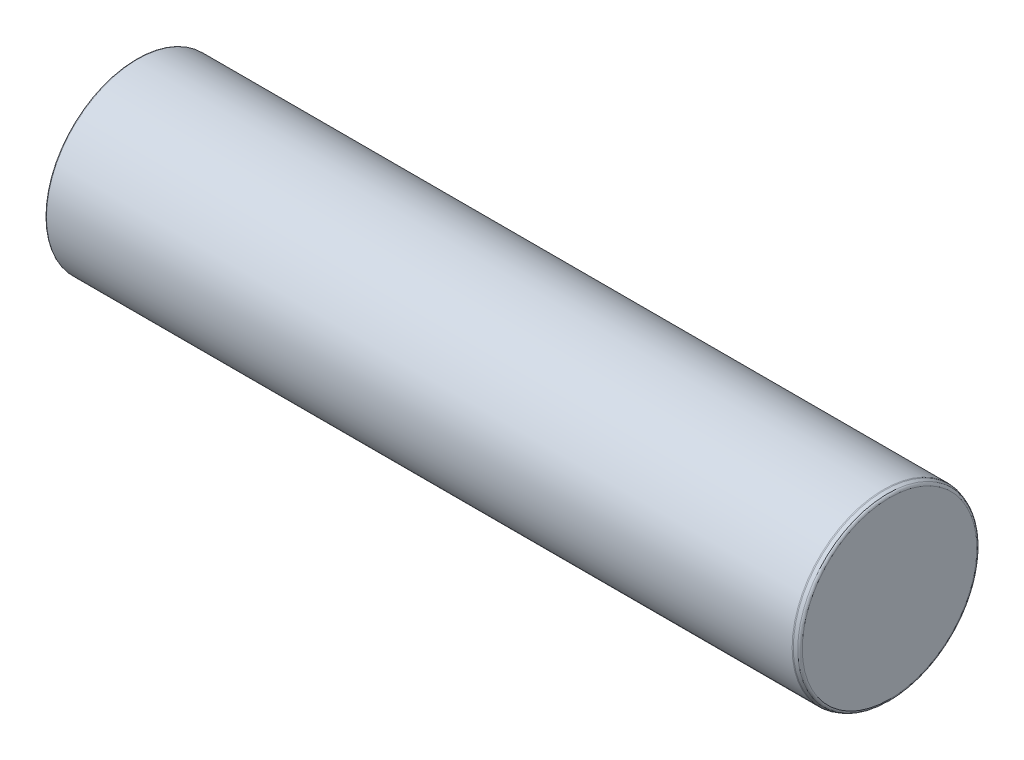
SolidWorks part; units mm, degrees
revolve "Base-Revolve" add sketch "Sketch1" angle 360 about L0
sketch "Sketch1" plane through (0, 0, 0) normal (0, 0, 1) x (1, 0, 0)
  line L0 (-136.5, 0) -> (136.5, 0) construction
  line L1 (134.3237, 32.5) -> (-0.0001, 32.5)
  line L4 (-113.5555, 0) -> (136.5, 0)
  line L5 (135.842, 32.0115) -> (134.6657, 32.4397)
  line L6 (-131.5, 32.1) -> (-131.5, 28.4)
  line L7 (-136.5, 5.1) -> (-116.5, 5.1)
  line L8 (-116.5, 5.1) -> (-113.5555, 0)
  line L13 (-0.0001, 32.5) -> (-131.1, 32.5)
  line L17 (-132.7, 24.8845) -> (-136.3, 22.8061)
  line L19 (-132.5, 28) -> (-132.5, 25.2309)
  line L20 (-136.5, 22.4597) -> (-136.5, 5.1)
  line L21 (-131.9, 28) -> (-132.5, 28)
  line L22 (136.5, 31.0719) -> (136.5, 0)
  arc A0 (136.5, 31.0719) -> (135.842, 32.0115) centre (135.5, 31.0719) ccw
  arc A1 (-131.9, 28) -> (-131.5, 28.4) centre (-131.9, 28.4) ccw
  arc A2 (134.6657, 32.4397) -> (134.3237, 32.5) centre (134.3237, 31.5) ccw
  arc A3 (-136.3, 22.8061) -> (-136.5, 22.4597) centre (-136.1, 22.4597) ccw
  arc A4 (-132.7, 24.8845) -> (-132.5, 25.2309) centre (-132.9, 25.2309) ccw
  arc A5 (-131.5, 32.1) -> (-131.1, 32.5) centre (-131.1, 32.1) cw
  point P5 (136.5, 31.7721)
  point P15 (134.5, 32.5)
  point P28 (-132.5, 25)
  point P31 (-131.5, 32.5)
  dimension "D11" = 50
  dimension "D17" = 1
  dimension "D19" = 0.4
  dimension "D3" = 2
  dimension "D4" = 20
  dimension "D5" = 273
  dimension "D7" = 5
  dimension "D8" = 1
  dimension "D9" = 56
  dimension "D10" = 30
  dimension "D12" = 65
  dimension "D13" = 131.5
  dimension "D20" = 10.2
  dimension "D21" = 20
  dimension "D22" = 60
cosmetic thread "Cosmetic Thread1"
cosmetic thread "Cosmetic Thread2"
ref_plane "Front" through (0, 0, 0) normal (0, 0, 1) x (1, 0, 0)
ref_plane "Top" through (0, 0, 0) normal (0, 1, 0) x (1, 0, 0)
ref_plane "Right" through (0, 0, 0) normal (1, 0, 0) x (0, 0, -1)
